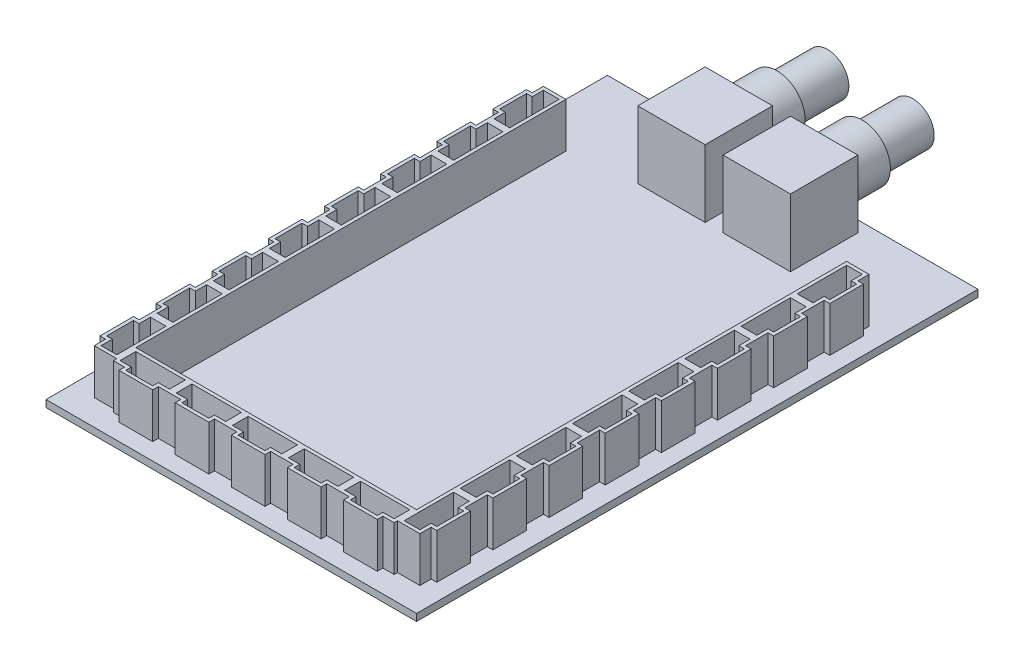
SolidWorks part; units mm, degrees
ref_plane "Front Plane" through (0, 0, 0) normal (0, 0, 1) x (1, 0, 0)
ref_plane "Top Plane" through (0, 0, 0) normal (0, 1, 0) x (1, 0, 0)
ref_plane "Right Plane" through (0, 0, 0) normal (1, 0, 0) x (0, 0, -1)
sketch "Sketch1" plane through (0, 0, 0) normal (0, 1, 0) x (1, 0, 0)
  line L1 (41.91, -63.5) -> (-41.91, -63.5)
  line L2 (41.91, -63.5) -> (41.91, 63.5)
  line L3 (41.91, 63.5) -> (-41.91, 63.5)
  line L4 (-41.91, -63.5) -> (-41.91, 63.5)
  line L5 (41.91, -63.5) -> (-41.91, 63.5) construction
  line L6 (41.91, 63.5) -> (-41.91, -63.5) construction
  point P0 (0, 0)
  dimension "D1" = 83.82
  dimension "D2" = 127
extrude "Boss-Extrude1" add sketch "Sketch1" along normal blind 1.5875
sketch "Sketch2" plane through (0, 1.5875, 0) normal (0, 1, 0) x (1, 0, 0)
  line L0 (-17.272, 45.72) -> (-41.91, 45.72) construction
  line L1 (-2.032, 45.72) -> (-17.272, 45.72)
  line L2 (-2.032, 45.72) -> (-2.032, 60.96)
  line L3 (-2.032, 60.96) -> (-17.272, 60.96)
  line L4 (-17.272, 45.72) -> (-17.272, 60.96)
  line L5 (2.032, 45.72) -> (17.272, 45.72)
  line L6 (2.032, 45.72) -> (2.032, 60.96)
  line L7 (2.032, 60.96) -> (17.272, 60.96)
  line L8 (17.272, 45.72) -> (17.272, 60.96)
  line L9 (-41.91, 63.5) -> (-41.91, -63.5) construction
  line L10 (41.91, 45.72) -> (17.272, 45.72) construction
  line L11 (41.91, -63.5) -> (41.91, 63.5) construction
  line L12 (41.91, 63.5) -> (-41.91, 63.5) construction
  dimension "D1" = 2.54
  dimension "D2" = 15.24
  dimension "D3" = 4.064
  dimension "D4" = 15.24
extrude "BNC Base" add sketch "Sketch2" along normal blind 15.24
sketch "Sketch3" plane through (0, 0, -60.96) normal (0, 0, -1) x (-1, 0, 0)
  line L0 (-9.652, 16.8275) -> (-9.652, 1.5875) construction
  line L1 (-17.272, 16.8275) -> (-2.032, 16.8275) construction
  line L2 (-17.272, 1.5875) -> (-2.032, 1.5875) construction
  line L3 (9.652, 16.8275) -> (9.652, 1.5875) construction
  line L4 (2.032, 16.8275) -> (17.272, 16.8275) construction
  line L5 (2.032, 1.5875) -> (17.272, 1.5875) construction
  circle A0 centre (-9.652, 9.2075) radius 6.35
  circle A1 centre (9.652, 9.2075) radius 6.35
  dimension "D1" = 12.7
extrude "BNC Shaft" add sketch "Sketch3" along normal blind 8.636
sketch "Sketch4" plane through (0, 0, -69.596) normal (0, 0, -1) x (-1, 0, 0)
  circle A0 centre (-9.652, 9.2075) radius 4.826
  circle A1 centre (-9.652, 9.2075) radius 4.191
  circle A2 centre (9.652, 9.2075) radius 4.826
  circle A3 centre (9.652, 9.2075) radius 4.191
  dimension "D1" = 9.652
  dimension "D2" = 8.382
extrude "BNC Shield" add sketch "Sketch4" along normal blind 11.43
sketch "Sketch5" plane through (0, 0, 0) normal (0, -1, 0) x (1, 0, 0)
  line L0 (41.91, -63.5) -> (-41.91, -63.5) construction
  line L1 (-25.3365, -16.256) -> (-22.9235, -16.256)
  line L2 (-25.3365, -16.256) -> (-25.3365, -32.004)
  line L3 (-25.3365, -32.004) -> (-22.9235, -32.004)
  line L4 (-22.9235, -16.256) -> (-22.9235, -32.004)
  line L5 (22.9235, -20.32) -> (25.3365, -20.32)
  line L6 (22.9235, -20.32) -> (22.9235, -41.148)
  line L7 (22.9235, -41.148) -> (25.3365, -41.148)
  line L8 (25.3365, -20.32) -> (25.3365, -41.148)
  line L9 (22.9235, 1.524) -> (22.9235, 3.556) construction
  line L10 (22.9235, -19.304) -> (25.3365, -19.304)
  line L11 (22.9235, -19.304) -> (22.9235, 1.524)
  line L12 (22.9235, 1.524) -> (25.3365, 1.524)
  line L13 (25.3365, -19.304) -> (25.3365, 1.524)
  line L14 (22.9235, 3.556) -> (25.3365, 3.556)
  line L15 (22.9235, 3.556) -> (22.9235, 24.384)
  line L16 (22.9235, 24.384) -> (25.3365, 24.384)
  line L17 (25.3365, 3.556) -> (25.3365, 24.384)
  line L18 (22.9235, -20.32) -> (22.9235, -19.304) construction
  line L19 (-22.9235, -28.5442) -> (22.9235, -28.5442) construction
  line L20 (0, -28.5442) -> (0, -63.5) construction
  line L21 (-25.3365, -16.256) -> (-25.3365, -14.224) construction
  line L22 (-25.3365, -14.224) -> (-22.9235, -14.224)
  line L23 (-25.3365, -14.224) -> (-25.3365, 6.604)
  line L24 (-25.3365, 6.604) -> (-22.9235, 6.604)
  line L25 (-22.9235, -14.224) -> (-22.9235, 6.604)
  line L26 (-25.3365, 8.636) -> (-22.9235, 8.636)
  line L27 (-25.3365, 8.636) -> (-25.3365, 29.464)
  line L28 (-25.3365, 29.464) -> (-22.9235, 29.464)
  line L29 (-22.9235, 8.636) -> (-22.9235, 29.464)
  line L30 (-25.3365, 6.604) -> (-25.3365, 8.636) construction
  dimension "D1" = 2.413
  dimension "D2" = 31.496
  dimension "D3" = 22.352
  dimension "D4" = 20.828
  dimension "D5" = 1.016
  dimension "D6" = 45.847
  dimension "D7" = 15.748
  dimension "D8" = 2.032
extrude "BaseHeaders" add sketch "Sketch5" along normal blind 2.413
sketch "Sketch6" plane through (0, 1.5875, 0) normal (0, 1, 0) x (1, 0, 0)
  line L0 (-36.83, 43.942) -> (-31.75, 43.942)
  line L1 (-31.75, 43.942) -> (-31.75, 31.242)
  line L2 (-31.75, 31.242) -> (-36.83, 31.242)
  line L3 (-36.83, 31.242) -> (-36.83, 33.782)
  line L4 (-36.83, 33.782) -> (-38.1, 33.782)
  line L5 (-38.1, 33.782) -> (-38.1, 41.402)
  line L6 (-38.1, 41.402) -> (-36.83, 41.402)
  line L7 (-36.83, 41.402) -> (-36.83, 43.942)
  line L8 (-37.338, 34.544) -> (-37.338, 40.64)
  line L9 (-37.338, 40.64) -> (-36.068, 40.64)
  line L10 (-36.068, 40.64) -> (-36.068, 43.18)
  line L11 (-36.068, 43.18) -> (-32.512, 43.18)
  line L12 (-32.512, 43.18) -> (-32.512, 32.004)
  line L13 (-32.512, 32.004) -> (-36.068, 32.004)
  line L14 (-36.068, 32.004) -> (-36.068, 34.544)
  line L15 (-36.068, 34.544) -> (-37.338, 34.544)
  line L16 (-34.29, 43.18) -> (-34.29, 40.64) construction
  line L17 (-34.29, 40.64) -> (-34.29, 38.1) construction
  line L18 (-34.29, 35.56) -> (-34.29, 38.1) construction
  line L19 (-34.29, 35.56) -> (-34.29, 33.02) construction
  line L20 (41.91, 63.5) -> (-41.91, 63.5) construction
  line L21 (-41.91, 63.5) -> (-41.91, -63.5) construction
  circle A0 centre (-34.29, 40.64) radius 0.381 construction
  circle A1 centre (-34.29, 38.1) radius 0.381 construction
  circle A2 centre (-34.29, 35.56) radius 0.381 construction
  circle A3 centre (-34.29, 33.02) radius 0.381 construction
  point P2 (-31.75, 37.592)
  dimension "D6" = 0.762
  dimension "D1" = 1.27
  dimension "D2" = 6.35
  dimension "D3" = 12.7
  dimension "D5" = 2.54
  dimension "D7" = 20.32
  dimension "D8" = 3.81
  dimension "D9" = 7.62
  dimension "D4" = 0.762
extrude "Boss-Extrude6" add sketch "Sketch6" along normal blind 10.16
pattern_linear "LPattern1" count 8 spacing 12.7 along (0, 0, 1) of "Boss-Extrude6"
mirror "Mirror1" about plane through (0, 0, 0) normal (1, 0, 0) of "LPattern1", "Boss-Extrude6"
sketch "Sketch7" plane through (0, 1.5875, 0) normal (0, 1, 0) x (1, 0, 0)
  line L0 (-31.75, -58.42) -> (-31.75, -53.34)
  line L1 (-31.75, -53.34) -> (-19.05, -53.34)
  line L2 (-19.05, -53.34) -> (-19.05, -58.42)
  line L3 (-19.05, -58.42) -> (-21.59, -58.42)
  line L4 (-21.59, -58.42) -> (-21.59, -59.69)
  line L5 (-21.59, -59.69) -> (-29.21, -59.69)
  line L6 (-29.21, -59.69) -> (-29.21, -58.42)
  line L7 (-29.21, -58.42) -> (-31.75, -58.42)
  line L8 (-22.352, -58.928) -> (-28.448, -58.928)
  line L9 (-28.448, -58.928) -> (-28.448, -57.658)
  line L10 (-28.448, -57.658) -> (-30.988, -57.658)
  line L11 (-30.988, -57.658) -> (-30.988, -54.102)
  line L12 (-30.988, -54.102) -> (-19.812, -54.102)
  line L13 (-19.812, -54.102) -> (-19.812, -57.658)
  line L14 (-19.812, -57.658) -> (-22.352, -57.658)
  line L15 (-22.352, -57.658) -> (-22.352, -58.928)
  line L16 (-30.988, -55.88) -> (-28.448, -55.88) construction
  line L17 (-28.448, -55.88) -> (-25.908, -55.88) construction
  line L18 (-23.368, -55.88) -> (-25.908, -55.88) construction
  line L19 (-23.368, -55.88) -> (-20.828, -55.88) construction
  line L20 (-41.91, 63.5) -> (-41.91, -63.5) construction
  line L21 (-41.91, -63.5) -> (41.91, -63.5) construction
  line L22 (-25.4, -59.69) -> (-25.4, -58.928) construction
  line L23 (-25.4, -54.102) -> (-25.4, -53.34) construction
  line L24 (-19.05, -55.88) -> (-19.812, -55.88) construction
  line L25 (-30.988, -55.88) -> (-31.75, -55.88) construction
  line L26 (-19.812, -57.658) -> (-19.812, -58.42) construction
  line L27 (-28.448, -58.928) -> (-29.21, -58.928) construction
  circle A0 centre (-28.448, -55.88) radius 0.381 construction
  circle A1 centre (-25.908, -55.88) radius 0.381 construction
  circle A2 centre (-23.368, -55.88) radius 0.381 construction
  circle A3 centre (-20.828, -55.88) radius 0.381 construction
  point P2 (-25.4, -53.34)
  dimension "D6" = 0.762
  dimension "D1" = 1.27
  dimension "D2" = 6.35
  dimension "D3" = 12.7
  dimension "D5" = 2.54
  dimension "D7" = 0.762
  dimension "D8" = 5.08
  dimension "D9" = 7.62
  dimension "D4" = 10.16
extrude "Boss-Extrude7" add sketch "Sketch7" along normal blind 10.16
pattern_linear "LPattern2" count 5 spacing 12.7 along (1, 0, 0) of "Boss-Extrude7"
